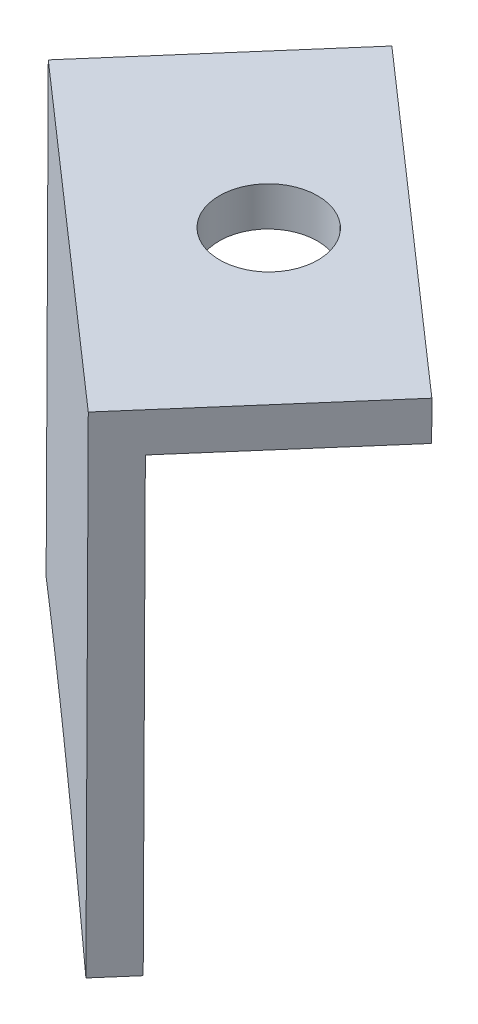
SolidWorks part; units mm, degrees
material "1.4105 (X6CrMoS17)"
ref_plane "Płaszczyzna XY" through (0, 0, 0) normal (0, 0, 1) x (1, 0, 0)
ref_plane "Płaszczyzna XZ" through (0, 0, 0) normal (0, 1, 0) x (1, 0, 0)
ref_plane "Płaszczyzna YZ" through (0, 0, 0) normal (1, 0, 0) x (0, 0, -1)
ref_plane "Płaszczyzna1" through (184.0502, 0, -211.7255) normal (0.6561, 0, -0.7547) x (-0.7547, 0, -0.6561)
sketch "Szkic1" plane through (184.0502, 0, -211.7255) normal (0.6561, 0, -0.7547) x (-0.7547, 0, -0.6561)
  line L2 (-722.6177, -314.1207) -> (-723.7859, -289.148)
  line L3 (-702.7408, -311.023) -> (-703.8077, -288.2135)
  line L5 (-723.7859, -289.148) -> (-703.8077, -288.2135)
  spline S0 degree 3 poles (-687.5461, -317.2444) (-680.7881, -341.3137) (-741.5185, -358.3652) (-748.2765, -334.296) (-755.0346, -310.2267) (-694.3042, -293.1752) (-687.5461, -317.2444) (-680.7881, -341.3137) (-741.5185, -358.3652) knots -0.5 0 0 0 0.5 0.5 0.5 1 1 1 1.5 1.5 1.5 weights 1 0.333333 0.333333 1 0.333333 0.333333 1 0.333333 0.333333 only from (-687.5461, -317.2444) to (-687.5461, -317.2444)
  spline S1 degree 3 poles (-722.6177, -314.1207) (-715.5816, -312.0125) (-708.7104, -310.9764) (-702.7408, -311.023) knots 0.74452 0.74452 0.74452 0.74452 0.831522 0.831522 0.831522 0.831522 weights 0.50024 0.497697 0.515339 0.553167
  dimension "D1" = 90
  dimension "D2" = 760.5343
  dimension "D3" = 25
  dimension "D4" = 20
  dimension "D5" = 779.4053
extrude "Dodanie-wyciągnięcie1" add sketch "Szkic1" along normal blind 2
ref_plane "Płaszczyzna2" through (185.3623, 0, -213.2349) normal (0.6561, 0, -0.7547) x (-0.7547, 0, -0.6561)
sketch "Szkic2" plane through (185.3623, 0, -213.2349) normal (0.6561, 0, -0.7547) x (-0.7547, 0, -0.6561)
  line L0 (-723.7859, -289.148) -> (-703.8077, -288.2135)
extrude "Wyciągnięcie-cienka ścianka1" add sketch "Szkic2" along normal blind 10 thin
ref_plane "Płaszczyzna3" through (-9.0634, -256.7318, -7.8787) normal (-0.0353, -0.9989, -0.0307) x (-0.9994, 0.0352, 0.0013)
sketch "Szkic3" plane through (-9.0634, -256.7318, -7.8787) normal (-0.0353, -0.9989, -0.0307) x (-0.9994, 0.0352, 0.0013)
  line L0 (-747.5614, -263.0061) -> (-732.4777, -249.8729) construction
  line L1 (-732.4777, -249.8729) -> (-725.9111, -257.4148) construction
  circle A0 centre (-736.7362, -260.2105) radius 2.5
  dimension "D1" = 5
  dimension "D2" = 5
  dimension "D3" = 10
extrude "Wytnij-wyciągnięcie1" cut sketch "Szkic3" against normal blind 10
